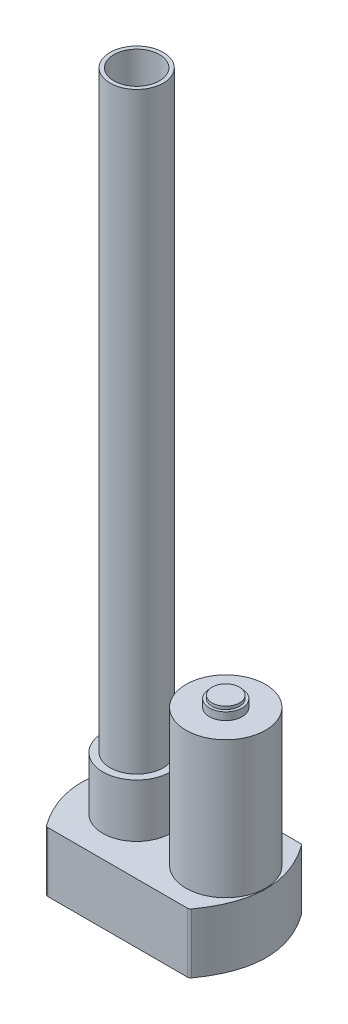
SolidWorks part; units mm, degrees
ref_plane "Front Plane" through (0, 0, 0) normal (0, 0, 1) x (1, 0, 0)
ref_plane "Top Plane" through (0, 0, 0) normal (0, 1, 0) x (1, 0, 0)
ref_plane "Right Plane" through (0, 0, 0) normal (1, 0, 0) x (0, 0, -1)
sketch "Sketch5" plane through (0, 0, 0) normal (0, 1, 0) x (1, 0, 0)
  line L2 (-52, -32) -> (42, -32)
  line L4 (-52, 42) -> (42, 42)
  spline S0 degree 2 poles (42, 42) (69.3, 5) (42, -32) knots 0 0 0 1 1 1
  spline S1 degree 2 poles (-52, 42) (-79.3, 5) (-52, -32) knots 0 0 0 1 1 1
  point P4 (1.6162, 5)
  point P11 (-44.4, 5)
  dimension "D1" = 94
  dimension "D2" = 74
extrude "Boss-Extrude3" add sketch "Sketch5" along normal blind 25 and the other way blind 14.3
sketch "Sketch6" plane through (0, 25, 0) normal (0, 1, 0) x (1, 0, 0)
  circle A1 centre (29.05, 5) radius 26.15
  point P0 (29.05, 5)
  dimension "D2" = 52.3
extrude "Boss-Extrude4" add sketch "Sketch6" along normal blind 90
sketch "Sketch7" plane through (0, 115, 0) normal (0, 1, 0) x (1, 0, 0)
  circle A0 centre (29.05, 5) radius 10.75
  circle A1 centre (29.05, 5) radius 8.15
  dimension "D1" = 21.5
  dimension "D2" = 16.3
extrude "Boss-Extrude5" add sketch "Sketch7" along normal blind 5
sketch "Sketch8" plane through (0, 115, 0) normal (0, 1, 0) x (1, 0, 0)
  circle A0 centre (29.05, 5) radius 9
  dimension "D1" = 18
extrude "Boss-Extrude6" add sketch "Sketch8" along normal blind 7
sketch "Sketch9" plane through (0, 25, 0) normal (0, 1, 0) x (1, 0, 0)
  line L0 (-51.8, 5) -> (-29.55, 5) construction
  line L1 (29.05, 5) -> (55.2, 5) construction
  circle A1 centre (-29.55, 5) radius 22.25
  circle A2 centre (-29.55, 5) radius 17.5
  circle A3 centre (29.05, 5) radius 26.15 construction
  circle A4 centre (29.05, 5) radius 26.15
  point P8 (-29.55, 5)
  dimension "D1" = 44.5
  dimension "D2" = 35
  dimension "D3" = 107
extrude "Boss-Extrude7" add sketch "Sketch9" along normal blind 35
sketch "Sketch10" plane through (0, 25, 0) normal (0, 1, 0) x (1, 0, 0)
  circle A0 centre (-29.55, 5) radius 17.5
  circle A1 centre (-29.55, 5) radius 15
  dimension "D1" = 35
  dimension "D2" = 30
extrude "Boss-Extrude8" add sketch "Sketch10" along normal blind 425
fillet "Fillet1" radius 2 4 edges at (42, 5.35, -42) (-52, 5.35, -42) (-52, 5.35, 32) (42, 5.35, 32)
